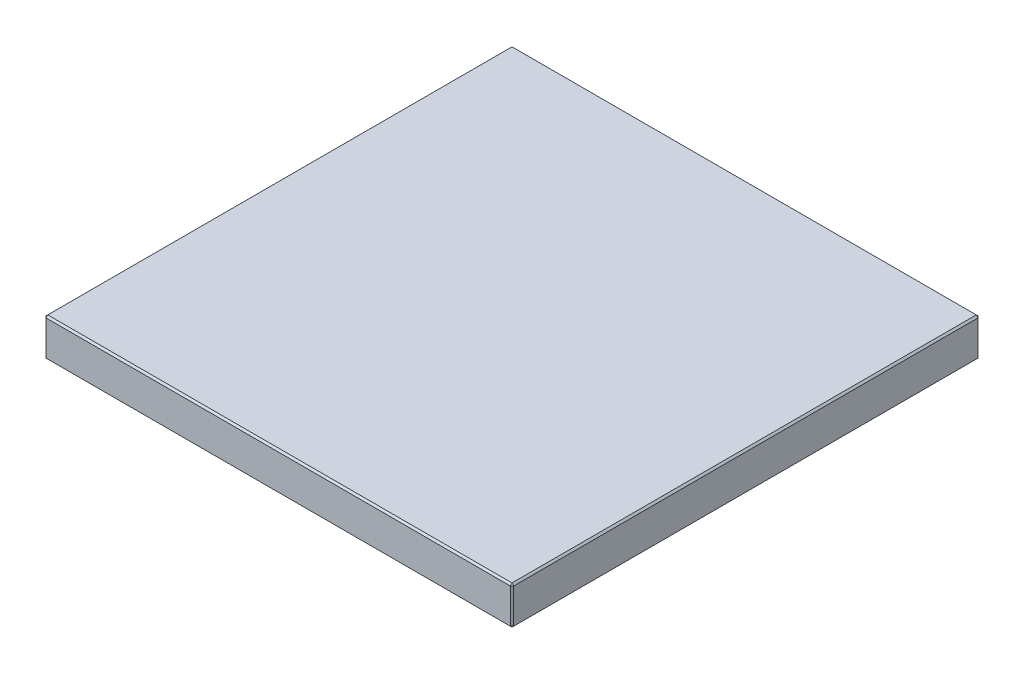
SolidWorks part; units mm, degrees
ref_plane "Front Plane" through (0, 0, 0) normal (0, 0, 1) x (1, 0, 0)
ref_plane "Top Plane" through (0, 0, 0) normal (0, 1, 0) x (1, 0, 0)
ref_plane "Right Plane" through (0, 0, 0) normal (1, 0, 0) x (0, 0, -1)
sketch "Sketch1" plane through (0, 0, 0) normal (0, 1, 0) x (1, 0, 0)
  line L1 (13.42, 13.42) -> (-13.42, 13.42)
  line L2 (13.42, 13.42) -> (13.42, -13.42)
  line L3 (13.42, -13.42) -> (-13.42, -13.42)
  line L4 (-13.42, 13.42) -> (-13.42, -13.42)
  line L5 (13.42, 13.42) -> (-13.42, -13.42) construction
  line L6 (13.42, -13.42) -> (-13.42, 13.42) construction
  point P0 (0, 0)
  dimension "D1" = 26.84
extrude "Boss-Extrude1" add sketch "Sketch1" along normal blind 2.2
chamfer "Chamfer1" distance 0.1 angle 45 12 edges at (-13.42, 1.1, -13.42) (-13.42, 1.1, 13.42) (13.42, 1.1, 13.42) (0, 0, 13.42) (13.42, 0, 0) (-13.42, 0, 0) (0, 0, -13.42) (13.42, 1.1, -13.42) (0, 2.2, -13.42) (13.42, 2.2, 0) (0, 2.2, 13.42) (-13.42, 2.2, 0)
ref_plane "Plane1" through (0, 0, 0) normal (0, 0, 1) x (1, 0, 0)
ref_plane "Plane2" through (0, 0, 0) normal (1, 0, 0) x (0, 0, -1)
